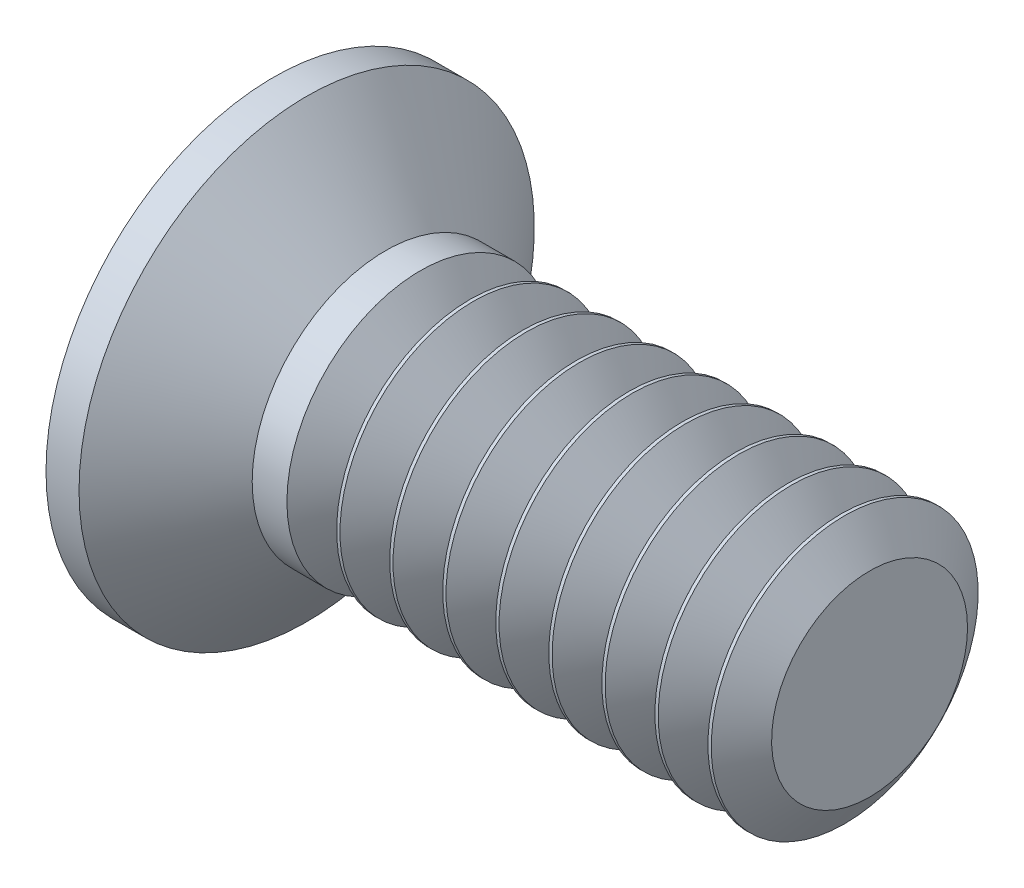
SolidWorks part; units mm, degrees
revolve "Base-Revolve" add sketch "BodySke" angle 360 about L5
sketch "BodySke" plane through (0, 0, 0) normal (0, 0, 1) x (1, 0, 0)
  line L0 (0, 0) -> (0, 2.4257)
  line L1 (0, 2.4257) -> (0.3519, 2.4257)
  line L2 (1.1938, 1.4224) -> (6.35, 1.4224)
  line L3 (6.35, 1.4224) -> (6.35, 0)
  line L4 (6.35, 0) -> (0, 0)
  line L5 (-6.35, 0) -> (82.55, 0) construction
  line L6 (1.1938, -1.4224) -> (6.35, -1.4224) construction
  line L7 (0.3519, -2.4257) -> (1.1938, -1.4224) construction
  line L8 (0.3519, 2.4257) -> (1.1938, 1.4224)
  line L9 (0, -2.4257) -> (0.3519, -2.4257) construction
  line L10 (1.8288, 3.0099) -> (1.8288, -6.5151) construction
  line L11 (0, 6.35) -> (0, -3.175) construction
  dimension "Diameter" = 2.8448
  dimension "Length" = 6.35
  dimension "Head_ht" = 1.1938
  dimension "Head_dia" = 4.8514
  dimension "Head_ang" = 100
  dimension "D6" = 0.3519
  dimension "Advance" = 0.635
  dimension "Thread_nom" = 6.35
cosmetic thread "ThreadCosmetic" [suppressed] parameters "Thread_length"=4.5212, "Thread_minor"=2.0879
extrude "Slot" [suppressed] cut sketch "Sketch2" against normal blind 0.6096
sketch "Sketch2" plane through (0, 0, 0) normal (-1, 0, 0) x (0, 0, 1)
  line L0 (-2.4257, -0.4953) -> (2.4257, -0.4953)
  line L1 (-2.4257, -0.4953) -> (-2.4257, 0.4953)
  line L2 (2.4257, 0.4953) -> (-2.4257, 0.4953)
  line L3 (2.4257, 0.4953) -> (2.4257, -0.4953)
  dimension "Slot_width" = 0.9906
  dimension "D1" = 0.4953
  dimension "D2" = 4.8514
  dimension "D3" = 2.4257
ref_plane "Plane1" through (0, 0, 0) normal (0, 0, 1) x (1, 0, 0)
ref_plane "Plane2" through (0, 0, 0) normal (0, 1, 0) x (1, 0, 0)
ref_plane "Plane3" through (0, 0, 0) normal (1, 0, 0) x (0, 0, -1)
sketch "Sketch3" plane through (0, 0, 0) normal (-1, 0, 0) x (0, 0, 1)
  line L0 (-0.3683, 1.7272) -> (0.3683, 1.7272)
  line L1 (0.3683, 1.7272) -> (0.3683, -1.7272)
  line L2 (0.3683, -1.7272) -> (-0.3683, -1.7272)
  line L3 (-0.3683, -1.7272) -> (-0.3683, 1.7272)
  dimension "Cross_dia" = 3.4544
  dimension "Cross_width" = 0.7366
  dimension "D1" = 1.7272
  dimension "D2" = 0.3683
ref_plane "Plane4" through (2.2606, 0, 0) normal (-1, 0, 0) x (0, 0, 1)
sketch "Sketch4" plane through (2.2606, 0, 0) normal (-1, 0, 0) x (0, 0, 1)
  line L0 (-0.1842, 0.1842) -> (0.1842, 0.1842)
  line L3 (0.1842, 0.1842) -> (0.1842, -0.1842)
  line L4 (0.1842, -0.1842) -> (-0.1841, -0.1842)
  line L5 (-0.1841, -0.1842) -> (-0.1842, 0.1842)
  dimension "D2" = 0.3683
  dimension "D1" = 0.3683
  dimension "D3" = 0.1842
  dimension "D4" = 0.1842
loft "Cross" cut profiles "Sketch3", "Sketch4"
pattern_circular "CirPattern1" count 2 every 90 about axis through (0, 0, 0) along (1, 0, 0) of "Cross"
sketch "ThdSchSke" plane through (0, 0, 0) normal (0, 0, 1) x (1, 0, 0)
  line L0 (1.8288, -1.0439) -> (1.5638, -1.4224)
  line L1 (1.8288, -1.0439) -> (2.0938, -1.4224)
  line L2 (2.0938, -1.4224) -> (2.0938, -1.778)
  line L3 (-3.175, 0) -> (5.1513, 0) construction
  line L5 (2.0938, -1.778) -> (1.5638, -1.778)
  line L6 (1.5638, -1.778) -> (1.5638, -1.4224)
  line L7 (0, 2.4257) -> (0, -2.4257) construction
  dimension "Diameter" = 2.8448
  dimension "Thread_minor" = 2.0879
  dimension "Start" = 1.8288
revolve "ThreadSchematic" cut sketch "ThdSchSke" angle 360 about L3
pattern_linear "ThdSchPat" count 9 spacing 0.5651 along (1, 0, 0) of "ThreadSchematic"
equation "\"D1@Sketch3\" = \"Cross_dia@Sketch3\" / 2"
equation "\"D2@Sketch3\" = \"Cross_width@Sketch3\" / 2"
equation "\"D1@Sketch4\" = \"Cross_width@Sketch3\" *.5"
equation "\"D2@Sketch4\" = \"D1@Sketch4\""
equation "\"D4@Sketch4\" = \"D2@Sketch4\" / 2"
equation "\"D3@Sketch4\" = \"D1@Sketch4\" / 2"
equation "\"D1@Sketch2\" = \"Slot_width@Sketch2\" / 2"
equation "\"D2@Sketch2\" = \"Head_dia@BodySke\""
equation "\"D3@Sketch2\" = \"D2@Sketch2\" / 2"
equation "\"Thread_length@ThreadCosmetic\" = ((sgn( (\"Length@BodySke\" - \"Advance@BodySke\" - \"Head_ht@BodySke\" ) - \"Thread_nom@BodySke\" )-1)*( (\"Length@BodySke\" - \"Advance@BodySke\" - \"Head_ht@BodySke\" ) - \"Thread_nom@BodySke\" ))/-2+ \"Thread_nom@BodySke\""
equation "\"Thread_minor@ThdSchSke\" = \"Thread_minor@ThreadCosmetic\""
equation "\"Diameter@ThdSchSke\" = \"Diameter@BodySke\""
equation "\"Overcut@ThdSchSke\" = \"Diameter@BodySke\" * 1.25"
equation "\"Start@ThdSchSke\" = 0.000001 + \"Length@BodySke\" - \"Thread_length@ThreadCosmetic\"  '---Countersunk---"
equation "\"Num_threads@ThdSchPat\" = int( \"Thread_length@ThreadCosmetic\" / \"Advance@BodySke\" + 0.999 )  + 1"
equation "\"Advance@ThdSchPat\" = \"Thread_length@ThreadCosmetic\" /  (\"Num_threads@ThdSchPat\" - 1) 'relax it"
